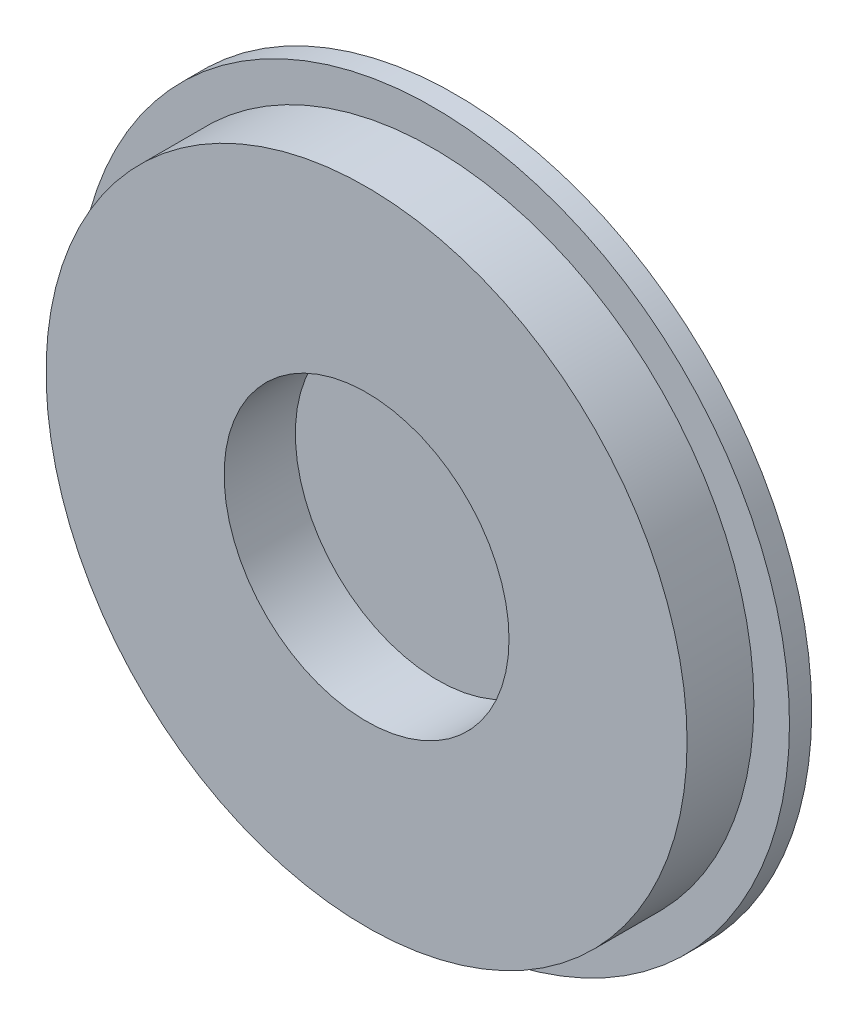
SolidWorks part; units mm, degrees
ref_plane "Front Plane" through (0, 0, 0) normal (0, 0, 1) x (1, 0, 0)
ref_plane "Top Plane" through (0, 0, 0) normal (0, 1, 0) x (1, 0, 0)
ref_plane "Right Plane" through (0, 0, 0) normal (1, 0, 0) x (0, 0, -1)
sketch "Sketch1" plane through (0, 0, 0) normal (0, 0, 1) x (1, 0, 0)
  circle A0 centre (0, 0) radius 20
  dimension "D1" = 40
extrude "Boss-Extrude1" add sketch "Sketch1" along normal blind 1.25
sketch "Sketch2" plane through (0, 0, 1.25) normal (0, 0, 1) x (1, 0, 0)
  circle A0 centre (0, 0) radius 18
  dimension "D1" = 36
extrude "Boss-Extrude2" add sketch "Sketch2" along normal blind 3.75
sketch "Sketch3" plane through (0, 0, 5) normal (0, 0, 1) x (1, 0, 0)
  circle A0 centre (0, 0) radius 8
  dimension "D1" = 16
extrude "Cut-Extrude1" cut sketch "Sketch3" against normal blind 4
